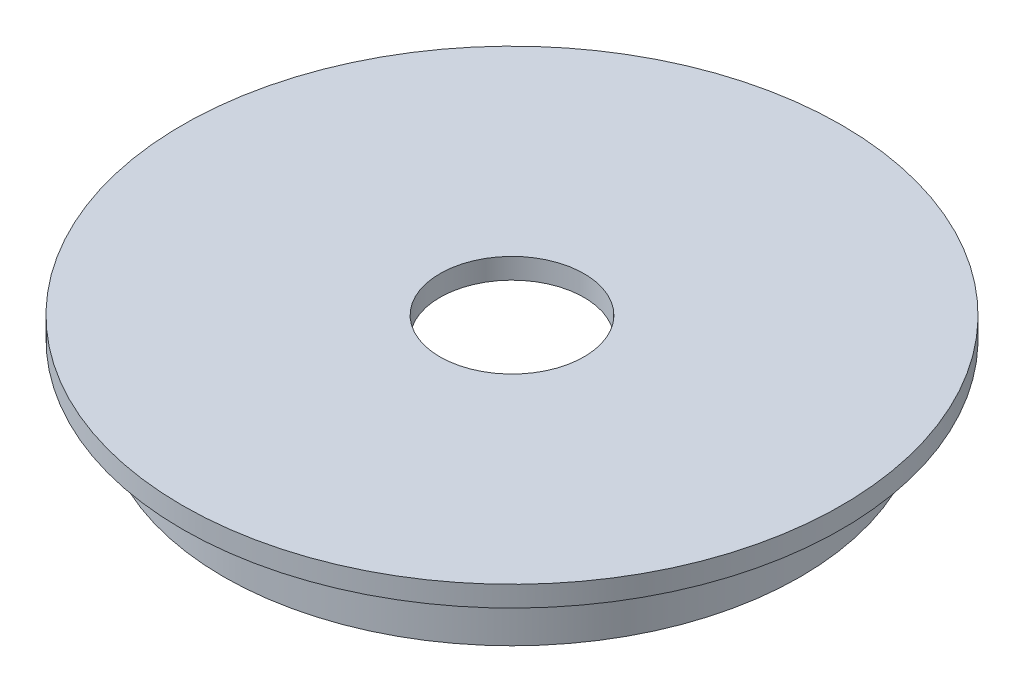
SolidWorks part; units mm, degrees
ref_plane "Front Plane" through (0, 0, 0) normal (0, 0, 1) x (1, 0, 0)
ref_plane "Top Plane" through (0, 0, 0) normal (0, 1, 0) x (1, 0, 0)
ref_plane "Right Plane" through (0, 0, 0) normal (1, 0, 0) x (0, 0, -1)
sketch "Sketch1" plane through (0, 0, 0) normal (0, 0, 1) x (1, 0, 0)
  line L0 (0, 0) -> (-50.8, 0)
  line L1 (-50.8, 0) -> (-50.8, -3.175)
  line L2 (-50.8, -3.175) -> (-44.45, -3.175)
  line L3 (-44.45, -3.175) -> (-44.45, -12.7)
  line L4 (-44.45, -12.7) -> (0, -12.7)
  line L5 (0, -12.7) -> (0, 0)
  dimension "D1" = 50.8
  dimension "D2" = 44.45
  dimension "D3" = 3.175
  dimension "D4" = 9.525
revolve "Revolve1" add sketch "Sketch1" angle 360 about L5
sketch "Sketch2" plane through (0, -12.7, 0) normal (0, -1, 0) x (1, 0, 0)
  circle A0 centre (0, 0) radius 41.275
  circle A1 centre (0, 0) radius 44.45 construction
  dimension "D1" = 3.175
extrude "Cut-Extrude1" cut sketch "Sketch2" against normal up to surface (9.525 mm away) up to face at (0, -3.175, -44.45)
sketch "Sketch3" plane through (0, 0, 0) normal (0, 1, 0) x (1, 0, 0)
  circle A0 centre (0, 0) radius 11.1125
  dimension "D1" = 22.225
extrude "Cut-Extrude2" cut sketch "Sketch3" against normal through all contours A0
